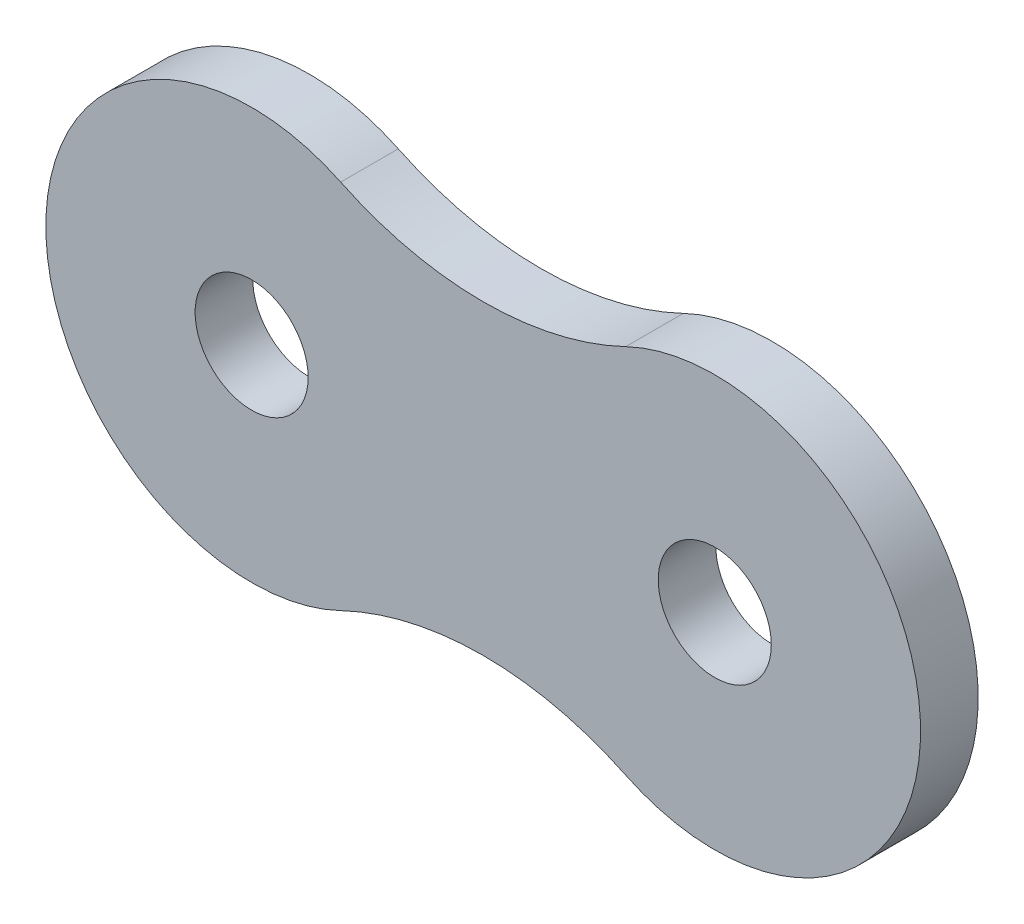
SolidWorks part; units mm, degrees
ref_plane "Plan de face" through (0, 0, 0) normal (0, 0, 1) x (1, 0, 0)
ref_plane "Plan de dessus" through (0, 0, 0) normal (0, 1, 0) x (1, 0, 0)
ref_plane "Plan de droite" through (0, 0, 0) normal (1, 0, 0) x (0, 0, -1)
sketch "Esquisse1" plane through (0, 0, 0) normal (0, 0, 1) x (1, 0, 0)
  arc A0 (-2.4423, -5.0888) -> (-2.4423, 5.0888) centre (0, 0) ccw
  arc A1 (-10.2577, 5.0888) -> (-10.2577, -5.0888) centre (-12.7, 0) ccw
  arc A2 (-10.2577, 5.0888) -> (-2.4423, 5.0888) centre (-6.35, 13.2308) ccw
  arc A3 (-2.4423, -5.0888) -> (-10.2577, -5.0888) centre (-6.35, -13.2308) ccw
  circle A4 centre (0, 0) radius 1.55
  circle A5 centre (-12.7, 0) radius 1.55
extrude "Extrusion1" add sketch "Esquisse1" along normal blind 1.58
